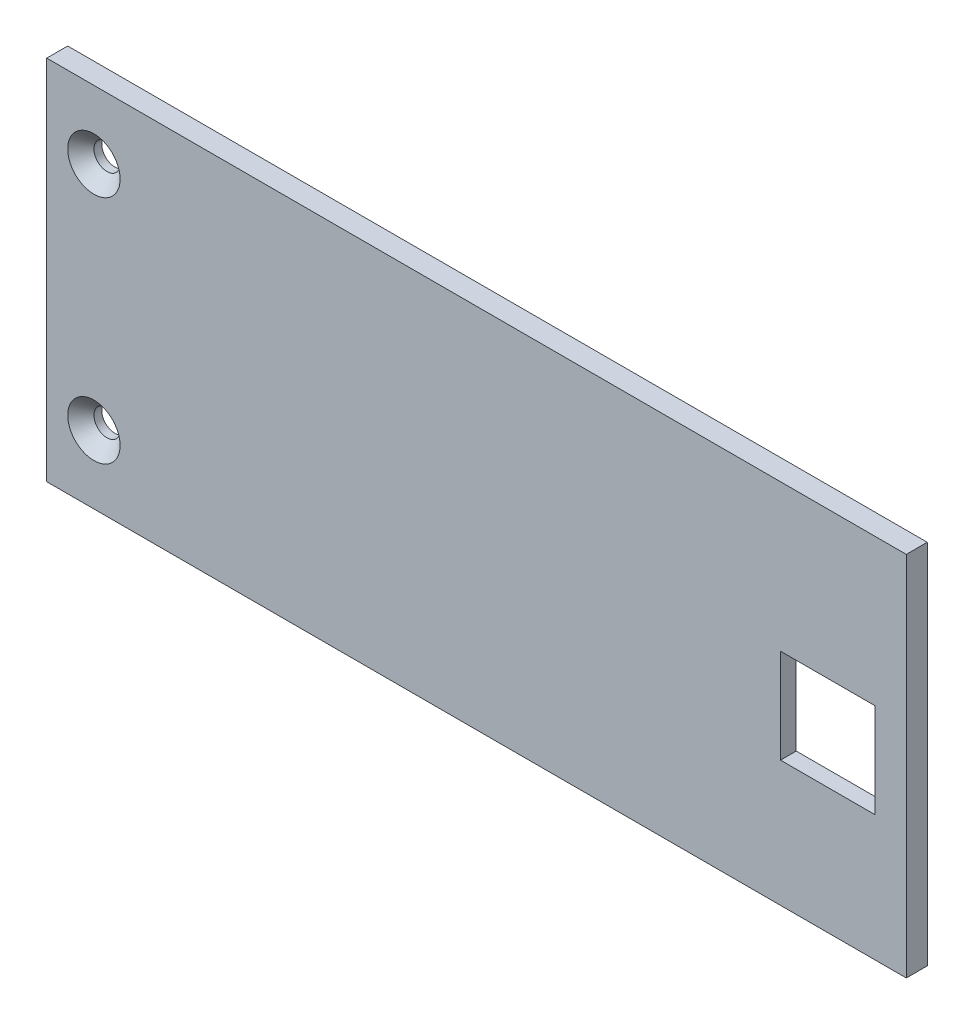
SolidWorks part; units mm, degrees
ref_plane "Plan de face" through (0, 0, 0) normal (0, 0, 1) x (1, 0, 0)
ref_plane "Plan de dessus" through (0, 0, 0) normal (0, 1, 0) x (1, 0, 0)
ref_plane "Plan de droite" through (0, 0, 0) normal (1, 0, 0) x (0, 0, -1)
sketch "Esquisse1" plane through (0, 0, 0) normal (0, 0, 1) x (1, 0, 0)
  line L0 (-77.5, 16.5) -> (-12, 16.5) construction
  line L1 (0, 0) -> (-82, 0)
  line L2 (0, 0) -> (0, 35)
  line L3 (0, 35) -> (-82, 35)
  line L4 (-82, 0) -> (-82, 35)
  line L5 (-77.5, 6.5) -> (-77.5, 28.5) construction
  line L6 (-12, 21) -> (-3, 21)
  line L7 (-12, 21) -> (-12, 16.5)
  line L8 (-12, 12) -> (-3, 12)
  line L9 (-3, 21) -> (-3, 12)
  line L11 (-7.5, 21) -> (-7.5, 23.6901) construction
  line L12 (-12, 16.5) -> (-12, 12)
  circle A0 centre (-77.5, 28.5) radius 1.25
  circle A1 centre (-77.5, 6.5) radius 1.25
  dimension "D3" = 2.5
  dimension "D1" = 82
  dimension "D2" = 35
  dimension "D4" = 22
  dimension "D5" = 4.5
  dimension "D6" = 9
  dimension "D7" = 9
  dimension "D8" = 7.5
  dimension "D9" = 18.5
  dimension "D10" = 6.5
extrude "Extrusion1" add sketch "Esquisse1" along normal blind 2
chamfer "Chanfrein1" distance 1.25 angle 45 2 edges at (-76.25, 28.5, 2) (-76.25, 6.5, 2)
sketch "Esquisse2" plane through (0, 0, 0) normal (0, 0, -1) x (-1, 0, 0)
  line L15 (2.5, 11.5) -> (12.5, 11.5)
  line L16 (2.5, 21.5) -> (2.5, 11.5)
  line L17 (12.5, 21.5) -> (2.5, 21.5)
  line L18 (12.5, 11.5) -> (12.5, 21.5)
  line L19 (2.5, 11.5) -> (12.5, 11.5)
  line L20 (2.5, 21.5) -> (2.5, 11.5)
  line L21 (12.5, 21.5) -> (2.5, 21.5)
  line L22 (12.5, 11.5) -> (12.5, 21.5)
  dimension "D1" = 0.5
extrude "Enlèv. mat.-Extru.1" cut sketch "Esquisse2" against normal blind 0.5
